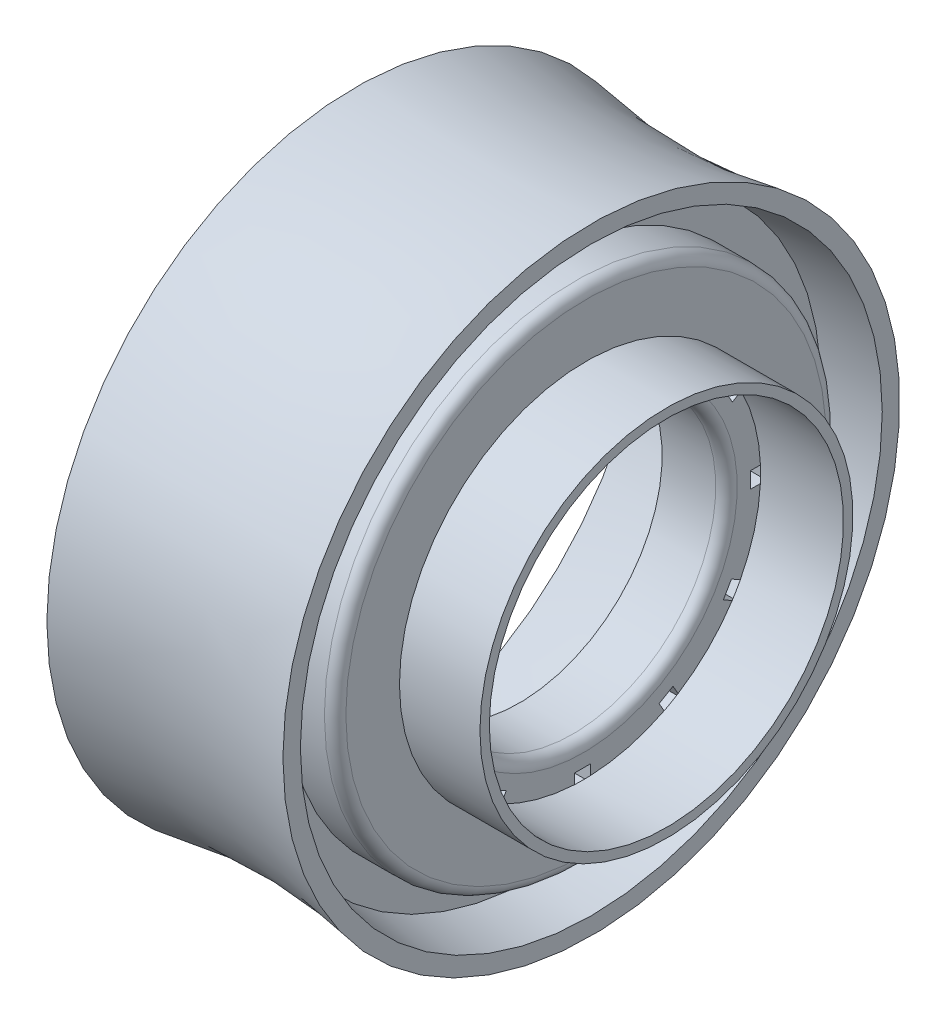
SolidWorks part; units mm, degrees
material "PE Low/Medium Density"
ref_plane "Front Plane" through (0, 0, 0) normal (0, 0, 1) x (1, 0, 0)
ref_plane "Top Plane" through (0, 0, 0) normal (0, 1, 0) x (1, 0, 0)
ref_plane "Right Plane" through (0, 0, 0) normal (1, 0, 0) x (0, 0, -1)
sketch "Sketch1" plane through (0, 0, 0) normal (0, 0, 1) x (1, 0, 0)
  line L0 (0, 0) -> (0, 14.605)
  line L1 (11.176, 14.605) -> (11.176, 0)
  line L2 (11.176, 0) -> (0, 0)
  line L3 (-10.4477, 0) -> (30.7208, 0) construction
  arc A0 (0, 14.605) -> (11.176, 14.605) centre (5.588, 43.2755) ccw
  dimension "D3" = 29.21
  dimension "D1" = 11.176
  dimension "D2" = 29.21
revolve "Revolve1" add sketch "Sketch1" angle 360 about L3
shell "Shell1" thickness 0.8128
sketch "Sketch2" plane through (0, 0, 0) normal (0, 0, 1) x (1, 0, 0)
  line L0 (-18.4028, 0) -> (31.2692, 0) construction
  line L1 (8.636, 13.4078) -> (8.636, 11.8789)
  line L2 (8.636, 11.8789) -> (10.922, 11.8789)
  line L3 (10.922, 11.8789) -> (10.922, 8.8309)
  line L4 (10.922, 8.8309) -> (14.732, 8.8309)
  line L5 (14.732, 8.8309) -> (14.732, 8.3857)
  line L6 (14.732, 8.3857) -> (10.8054, 8.3857)
  line L7 (10.8054, 8.3857) -> (10.8054, 7.2798)
  line L8 (10.2974, 6.7718) -> (7.7574, 6.7718)
  line L9 (7.7574, 6.7718) -> (7.7574, 7.2798)
  line L10 (7.7574, 7.2798) -> (10.0778, 7.2798)
  line L11 (10.2974, 7.4994) -> (10.2974, 8.3857)
  line L12 (10.2974, 8.3857) -> (6.7414, 8.3857)
  line L13 (6.7414, 8.3857) -> (6.7414, 8.8309)
  line L14 (6.7414, 8.8309) -> (10.2974, 8.8309)
  line L15 (10.2974, 8.8309) -> (10.2974, 11.4123)
  line L16 (10.2974, 11.4123) -> (8.128, 11.4123)
  line L17 (8.128, 11.4123) -> (8.128, 13.3604)
  line L18 (11.176, -14.605) -> (11.176, 14.605) construction
  arc A0 (0, 13.7773) -> (11.176, 13.7773) centre (5.588, 43.2755) ccw construction
  arc A1 (10.8054, 7.2798) -> (10.2974, 6.7718) centre (10.2974, 7.2798) cw
  arc A2 (10.0778, 7.2798) -> (10.2974, 7.4994) centre (10.0778, 7.4994) ccw
  arc A5 (8.128, 13.3604) -> (8.636, 13.4078) centre (5.588, 43.2755) ccw
  point P34 (10.922, 10.3549)
  dimension "D5" = 0.4666
  dimension "D15" = 0.2197
  dimension "D1" = 1.5289
  dimension "D2" = 2.286
  dimension "D3" = 0.508
  dimension "D4" = 0.254
  dimension "D6" = 0.6246
  dimension "D7" = 3.048
  dimension "D8" = 0.4452
  dimension "D9" = 3.81
  dimension "D10" = 3.556
  dimension "D11" = 1.016
  dimension "D12" = 0.508
  dimension "D13" = 0.508
  dimension "D14" = 1.1059
revolve "Revolve2" add sketch "Sketch2" angle 360 about L0
fillet "Fillet1" radius 0.508 1 edges at (10.922, 0, 11.8789)
sketch "Sketch3" plane through (10.8054, 0, 0) normal (1, 0, 0) x (0, 0, -1)
  line L0 (4.0389, 7.6659) -> (3.6579, 7.006)
  line L1 (-0.3352, 8.6583) -> (0.4268, 8.6583)
  line L2 (-0.3352, 8.6583) -> (-0.3352, 7.8963)
  line L3 (-0.3352, 7.8963) -> (0.4268, 7.8963)
  line L4 (0.4268, 8.6583) -> (0.4268, 7.8963)
  line L5 (-0.3352, 8.6583) -> (0.4268, 7.8963) construction
  line L6 (-0.3352, 7.8963) -> (0.4268, 8.6583) construction
  line L7 (4.0389, 7.6659) -> (4.6988, 7.2849)
  line L8 (4.6988, 7.2849) -> (4.3178, 6.625)
  line L9 (3.6579, 7.006) -> (4.3178, 6.625)
  line L10 (7.3307, 4.6195) -> (6.6708, 4.2385)
  line L11 (7.3307, 4.6195) -> (7.7117, 3.9596)
  line L12 (7.7117, 3.9596) -> (7.0518, 3.5786)
  line L13 (6.6708, 4.2385) -> (7.0518, 3.5786)
  line L14 (8.6583, 0.3352) -> (7.8963, 0.3352)
  line L15 (8.6583, 0.3352) -> (8.6583, -0.4268)
  line L16 (8.6583, -0.4268) -> (7.8963, -0.4268)
  line L17 (7.8963, 0.3352) -> (7.8963, -0.4268)
  line L18 (7.6659, -4.0389) -> (7.006, -3.6579)
  line L19 (7.6659, -4.0389) -> (7.2849, -4.6988)
  line L20 (7.2849, -4.6988) -> (6.625, -4.3178)
  line L21 (7.006, -3.6579) -> (6.625, -4.3178)
  line L22 (4.6195, -7.3307) -> (4.2385, -6.6708)
  line L23 (4.6195, -7.3307) -> (3.9596, -7.7117)
  line L24 (3.9596, -7.7117) -> (3.5786, -7.0518)
  line L25 (4.2385, -6.6708) -> (3.5786, -7.0518)
  line L26 (0.3352, -8.6583) -> (0.3352, -7.8963)
  line L27 (0.3352, -8.6583) -> (-0.4268, -8.6583)
  line L28 (-0.4268, -8.6583) -> (-0.4268, -7.8963)
  line L29 (0.3352, -7.8963) -> (-0.4268, -7.8963)
  line L30 (-4.0389, -7.6659) -> (-3.6579, -7.006)
  line L31 (-4.0389, -7.6659) -> (-4.6988, -7.2849)
  line L32 (-4.6988, -7.2849) -> (-4.3178, -6.625)
  line L33 (-3.6579, -7.006) -> (-4.3178, -6.625)
  line L34 (-7.3307, -4.6195) -> (-6.6708, -4.2385)
  line L35 (-7.3307, -4.6195) -> (-7.7117, -3.9596)
  line L36 (-7.7117, -3.9596) -> (-7.0518, -3.5786)
  line L37 (-6.6708, -4.2385) -> (-7.0518, -3.5786)
  line L38 (-8.6583, -0.3352) -> (-7.8963, -0.3352)
  line L39 (-8.6583, -0.3352) -> (-8.6583, 0.4268)
  line L40 (-8.6583, 0.4268) -> (-7.8963, 0.4268)
  line L41 (-7.8963, -0.3352) -> (-7.8963, 0.4268)
  line L42 (-7.6659, 4.0389) -> (-7.006, 3.6579)
  line L43 (-7.6659, 4.0389) -> (-7.2849, 4.6988)
  line L44 (-7.2849, 4.6988) -> (-6.625, 4.3178)
  line L45 (-7.006, 3.6579) -> (-6.625, 4.3178)
  line L46 (-4.6195, 7.3307) -> (-4.2385, 6.6708)
  line L47 (-4.6195, 7.3307) -> (-3.9596, 7.7117)
  line L48 (-3.9596, 7.7117) -> (-3.5786, 7.0518)
  line L49 (-4.2385, 6.6708) -> (-3.5786, 7.0518)
  point P0 (0.0458, 8.2773)
  point P52 (0, 0)
  dimension "D1" = 0.762
  dimension "D2" = 0.762
  dimension "D3" = 12
extrude "Cut-Extrude1" cut sketch "Sketch3" against normal blind 1.016
